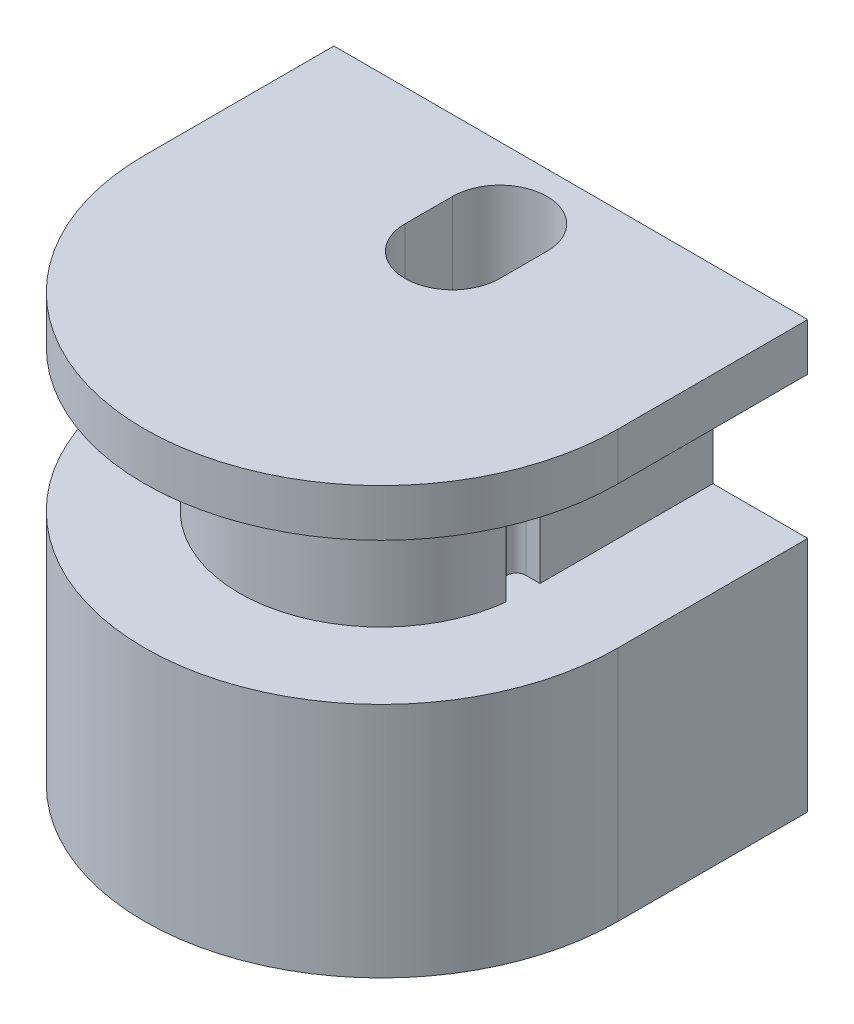
SolidWorks part; units mm, degrees
ref_plane "Plan de face" through (0, 0, 0) normal (0, 0, 1) x (1, 0, 0)
ref_plane "Plan de dessus" through (0, 0, 0) normal (0, 1, 0) x (1, 0, 0)
ref_plane "Plan de droite" through (0, 0, 0) normal (1, 0, 0) x (0, 0, -1)
sketch "Esquisse1" plane through (0, 0, 0) normal (0, 1, 0) x (1, 0, 0)
  line L1 (-5, 0) -> (5, 0)
  line L2 (-5, 0) -> (-5, -4)
  line L4 (5, 0) -> (5, -4)
  arc A0 (-5, -4) -> (5, -4) centre (0, -4) ccw
  dimension "D1" = 10
  dimension "D2" = 4
extrude "Extrusion1" add sketch "Esquisse1" along normal blind 5
sketch "Esquisse2" plane through (0, 5, 0) normal (0, 1, 0) x (1, 0, 0)
  line L0 (5, 0) -> (-5, 0) construction
  line L1 (-3, 0) -> (3, 0)
  line L2 (-3, 0) -> (-3, -4)
  line L4 (3, 0) -> (3, -4)
  arc A0 (-3, -4) -> (3, -4) centre (0, -4) ccw
  dimension "D1" = 3
  dimension "D2" = 4
extrude "Extrusion2" add sketch "Esquisse2" along normal blind 3
sketch "Esquisse3" plane through (0, 8, 0) normal (0, 1, 0) x (1, 0, 0)
  line L1 (-5, 0) -> (5, 0)
  line L2 (-5, 0) -> (-5, -4)
  line L4 (5, 0) -> (5, -4)
  arc A0 (-5, -4) -> (5, -4) centre (0, -4) ccw
  dimension "D1" = 10
  dimension "D2" = 4
extrude "Extrusion3" add sketch "Esquisse3" along normal blind 1
sketch "Esquisse4" plane through (0, 9, 0) normal (0, 1, 0) x (1, 0, 0)
  line L0 (0, -1.5) -> (0, -2.5) construction
  line L1 (1, -1.5) -> (1, -2.5)
  line L2 (-1, -1.5) -> (-1, -2.5)
  arc A0 (1, -1.5) -> (-1, -1.5) centre (0, -1.5) ccw
  arc A1 (-1, -2.5) -> (1, -2.5) centre (0, -2.5) ccw
  point P3 (0, -2)
  dimension "D1" = 1
  dimension "D2" = 1
  dimension "D3" = 2
extrude "Extrusion4" cut sketch "Esquisse4" against normal through all
sketch "Esquisse5" plane through (3, 0, 0) normal (1, 0, 0) x (0, 0, -1)
  line L0 (-4, 8) -> (0, 8) construction
  line L1 (-3.65, 8) -> (-4.35, 8)
  line L2 (-3.65, 8) -> (-3.65, 5)
  line L3 (-3.65, 5) -> (-4.35, 5)
  line L4 (-4.35, 8) -> (-4.35, 5)
  line L5 (-4, 5) -> (-9, 5) construction
  line L6 (-4, 8) -> (-4, 5) construction
  dimension "D1" = 0.7
  dimension "D2" = 0.35
extrude "Extrusion5" cut sketch "Esquisse5" against normal blind 0.5
fillet "Congé1" radius 0.2 2 edges at (2.5, 6.5, 3.65) (2.5, 6.5, 4.35)
